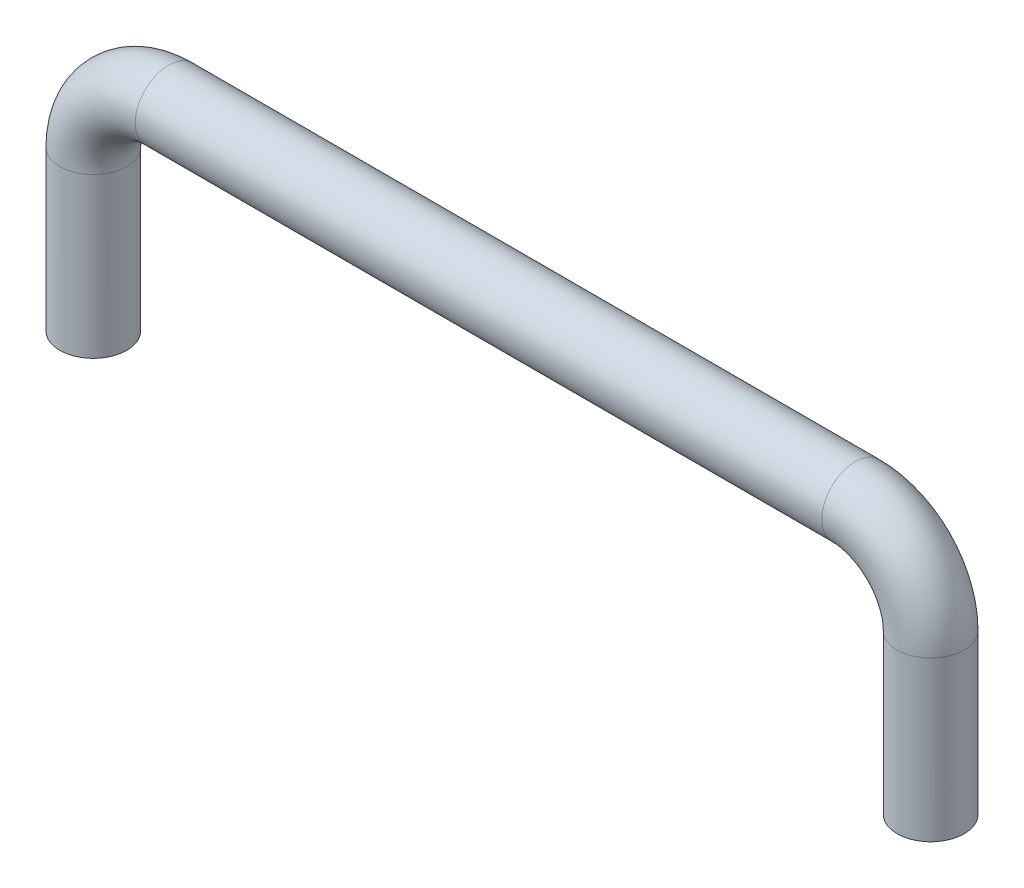
SolidWorks part; units mm, degrees
ref_plane "Plane1" through (0, 0, 0) normal (0, 0, 1) x (1, 0, 0)
ref_plane "Plane2" through (0, 0, 0) normal (0, 1, 0) x (1, 0, 0)
ref_plane "Plane3" through (0, 0, 0) normal (1, 0, 0) x (0, 0, -1)
sketch "Sketch1" plane through (0, 0, 0) normal (0, 0, 1) x (1, 0, 0)
  line L0 (0, 0) -> (0, 19)
  line L1 (9, 28) -> (91, 28)
  line L2 (100, 19) -> (100, 0)
  arc A0 (0, 19) -> (9, 28) centre (9, 19) cw
  arc A1 (91, 28) -> (100, 19) centre (91, 19) cw
  dimension "D3" = 9
  dimension "D1" = 100
  dimension "D2" = 28
ref_plane "Plane4" through (0, 0, 0) normal (0, 1, 0) x (-1, 0, 0)
sketch "Sketch2" plane through (0, 0, 0) normal (0, 1, 0) x (-1, 0, 0)
  circle A0 centre (0, 0) radius 4
  dimension "D1" = 8
sweep "Sweep1" add profiles "Sketch2" path "Sketch1"
